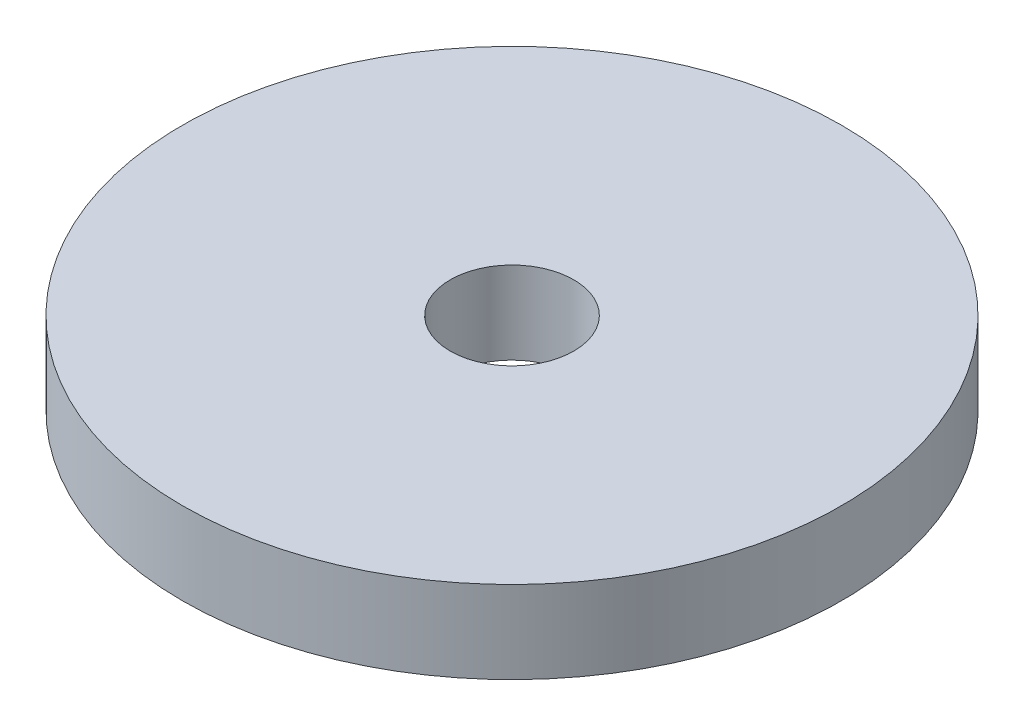
SolidWorks part; units mm, degrees
ref_plane "Front Plane" through (0, 0, 0) normal (0, 0, 1) x (1, 0, 0)
ref_plane "Top Plane" through (0, 0, 0) normal (0, 1, 0) x (1, 0, 0)
ref_plane "Right Plane" through (0, 0, 0) normal (1, 0, 0) x (0, 0, -1)
sketch "Sketch1" plane through (0, 0, 0) normal (0, 1, 0) x (1, 0, 0)
  circle A0 centre (0, 0) radius 4.7625
  circle A1 centre (0, 0) radius 25.4
  dimension "D1" = 9.525
  dimension "D2" = 50.8
extrude "Boss-Extrude1" add sketch "Sketch1" along normal blind 6.35
